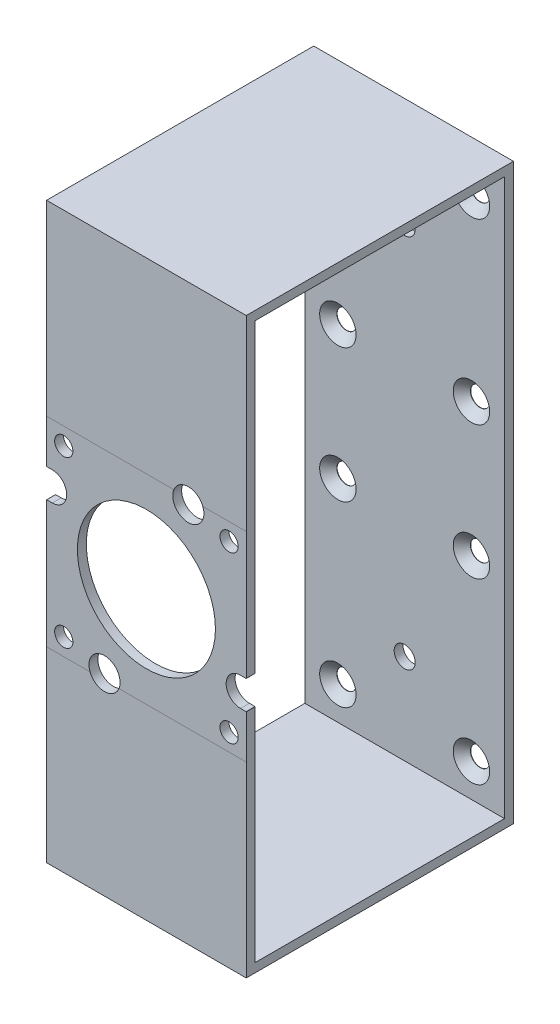
SolidWorks part; units mm, degrees
material "201 Annealed Stainless Steel (SS)"
ref_plane "Front Plane" through (0, 0, 0) normal (0, 0, 1) x (1, 0, 0)
ref_plane "Top Plane" through (0, 0, 0) normal (0, 1, 0) x (1, 0, 0)
ref_plane "Right Plane" through (0, 0, 0) normal (1, 0, 0) x (0, 0, -1)
sketch "Sketch2" plane through (0, 0, -4.819) normal (0, 0, -1) x (-1, 0, 0)
  circle A0 centre (-23.5732, -23.5732) radius 2.6 construction
  circle A1 centre (-23.5732, 23.5732) radius 2.6 construction
  circle A2 centre (23.5732, 23.5732) radius 2.6 construction
  circle A3 centre (23.5732, -23.5732) radius 2.6 construction
  circle A4 centre (-23.5732, -23.5732) radius 2.6
  circle A5 centre (-23.5732, 23.5732) radius 2.6
  circle A6 centre (23.5732, 23.5732) radius 2.6
  circle A7 centre (23.5732, -23.5732) radius 2.6
sketch "Sketch3" plane through (0, 0, -4.819) normal (0, 0, -1) x (-1, 0, 0)
  line L16 (28.4405, 7.8549) -> (26.8396, 7.8549)
  line L17 (26.8396, 16.0446) -> (28.4405, 16.0446)
  line L18 (28.4754, 16.0794) -> (28.4754, 25.845)
  line L19 (25.845, 28.4754) -> (-7.8201, 28.4754)
  line L20 (-7.8549, 28.4405) -> (-7.8549, 26.8396)
  line L21 (-16.0446, 26.8396) -> (-16.0446, 28.4405)
  line L22 (-16.0794, 28.4754) -> (-25.845, 28.4754)
  line L23 (-28.4754, 25.845) -> (-28.4754, -7.8201)
  line L24 (-28.4405, -7.8549) -> (-26.8396, -7.8549)
  line L25 (-26.8396, -16.0446) -> (-28.4405, -16.0446)
  line L26 (-28.4754, -16.0794) -> (-28.4754, -25.845)
  line L27 (-25.845, -28.4754) -> (7.8201, -28.4754)
  line L28 (7.8549, -28.4405) -> (7.8549, -26.8396)
  line L29 (16.0446, -26.8396) -> (16.0446, -28.4405)
  line L30 (16.0794, -28.4754) -> (25.845, -28.4754)
  line L31 (28.4754, -25.845) -> (28.4754, 7.8201)
  line L32 (28.4405, 7.8549) -> (26.8396, 7.8549)
  line L33 (26.8396, 16.0446) -> (28.4405, 16.0446)
  line L34 (28.4754, 16.0794) -> (28.4754, 25.845)
  line L35 (25.845, 28.4754) -> (-7.8201, 28.4754)
  line L36 (-7.8549, 28.4405) -> (-7.8549, 26.8396)
  line L37 (-16.0446, 26.8396) -> (-16.0446, 28.4405)
  line L38 (-16.0794, 28.4754) -> (-25.845, 28.4754)
  line L39 (-28.4754, 25.845) -> (-28.4754, -7.8201)
  line L40 (-28.4405, -7.8549) -> (-26.8396, -7.8549)
  line L41 (-26.8396, -16.0446) -> (-28.4405, -16.0446)
  line L42 (-28.4754, -16.0794) -> (-28.4754, -25.845)
  line L43 (-25.845, -28.4754) -> (7.8201, -28.4754)
  line L44 (7.8549, -28.4405) -> (7.8549, -26.8396)
  line L45 (16.0446, -26.8396) -> (16.0446, -28.4405)
  line L46 (16.0794, -28.4754) -> (25.845, -28.4754)
  line L47 (28.4754, -25.845) -> (28.4754, 7.8201)
  arc A8 (26.8396, 16.0446) -> (26.8396, 7.8549) centre (26.8396, 11.9498) ccw
  arc A9 (28.4754, 25.845) -> (25.845, 28.4754) centre (25.845, 25.845) ccw
  arc A10 (-16.0446, 26.8396) -> (-7.8549, 26.8396) centre (-11.9498, 26.8396) ccw
  arc A11 (-25.845, 28.4754) -> (-28.4754, 25.845) centre (-25.845, 25.845) ccw
  arc A12 (-26.8396, -16.0446) -> (-26.8396, -7.8549) centre (-26.8396, -11.9498) ccw
  arc A13 (-28.4754, -25.845) -> (-25.845, -28.4754) centre (-25.845, -25.845) ccw
  arc A14 (16.0446, -26.8396) -> (7.8549, -26.8396) centre (11.9498, -26.8396) ccw
  arc A15 (25.845, -28.4754) -> (28.4754, -25.845) centre (25.845, -25.845) ccw
  arc A16 (26.8396, 16.0446) -> (26.8396, 7.8549) centre (26.8396, 11.9498) ccw
  arc A17 (28.4754, 25.845) -> (25.845, 28.4754) centre (25.845, 25.845) ccw
  arc A18 (-16.0446, 26.8396) -> (-7.8549, 26.8396) centre (-11.9498, 26.8396) ccw
  arc A19 (-25.845, 28.4754) -> (-28.4754, 25.845) centre (-25.845, 25.845) ccw
  arc A20 (-26.8396, -16.0446) -> (-26.8396, -7.8549) centre (-26.8396, -11.9498) ccw
  arc A21 (-28.4754, -25.845) -> (-25.845, -28.4754) centre (-25.845, -25.845) ccw
  arc A22 (16.0446, -26.8396) -> (7.8549, -26.8396) centre (11.9498, -26.8396) ccw
  arc A23 (25.845, -28.4754) -> (28.4754, -25.845) centre (25.845, -25.845) ccw
  spline S8 degree 3 poles (-2168.2373, 2050.6322) (2176.4935, -2088.8807) (-2068.2203, 2155.8351) (2071.1385, -2188.738) knots -81.330068 -81.330068 -81.330068 -81.330068 81.328574 81.328574 81.328574 81.328574 only from (28.4754, 7.8201) to (28.4405, 7.8549)
  spline S9 degree 3 poles (2071.2526, 2212.7572) (-2068.2603, -2131.9736) (2176.4555, 2112.7403) (-2168.1176, -2026.6186) knots -78.188475 -78.188475 -78.188475 -78.188475 84.470167 84.470167 84.470167 84.470167 only from (28.4405, 16.0446) to (28.4754, 16.0794)
  spline S10 degree 3 poles (-2050.6322, -2168.2373) (2088.8807, 2176.4935) (-2155.8351, -2068.2203) (2188.738, 2071.1385) knots -81.330068 -81.330068 -81.330068 -81.330068 81.328574 81.328574 81.328574 81.328574 only from (-7.8201, 28.4754) to (-7.8549, 28.4405)
  spline S11 degree 3 poles (-2212.7572, 2071.2526) (2131.9736, -2068.2603) (-2112.7403, 2176.4555) (2026.6186, -2168.1176) knots -78.188475 -78.188475 -78.188475 -78.188475 84.470167 84.470167 84.470167 84.470167 only from (-16.0446, 28.4405) to (-16.0794, 28.4754)
  spline S12 degree 3 poles (2168.2373, -2050.6322) (-2176.4935, 2088.8807) (2068.2203, -2155.8351) (-2071.1385, 2188.738) knots -81.330068 -81.330068 -81.330068 -81.330068 81.328574 81.328574 81.328574 81.328574 only from (-28.4754, -7.8201) to (-28.4405, -7.8549)
  spline S13 degree 3 poles (-2071.2526, -2212.7572) (2068.2603, 2131.9736) (-2176.4555, -2112.7403) (2168.1176, 2026.6186) knots -78.188475 -78.188475 -78.188475 -78.188475 84.470167 84.470167 84.470167 84.470167 only from (-28.4405, -16.0446) to (-28.4754, -16.0794)
  spline S14 degree 3 poles (2050.6322, 2168.2373) (-2088.8807, -2176.4935) (2155.8351, 2068.2203) (-2188.738, -2071.1385) knots -81.330068 -81.330068 -81.330068 -81.330068 81.328574 81.328574 81.328574 81.328574 only from (7.8201, -28.4754) to (7.8549, -28.4405)
  spline S15 degree 3 poles (2212.7572, -2071.2526) (-2131.9736, 2068.2603) (2112.7403, -2176.4555) (-2026.6186, 2168.1176) knots -78.188475 -78.188475 -78.188475 -78.188475 84.470167 84.470167 84.470167 84.470167 only from (16.0446, -28.4405) to (16.0794, -28.4754)
  spline S16 degree 3 poles (28.4754, 7.8201) (28.4758, 7.8387) (28.4591, 7.8554) (28.4405, 7.8549) knots -0.784789 -0.784789 -0.784789 -0.784789 0.784789 0.784789 0.784789 0.784789
  spline S17 degree 3 poles (28.4405, 16.0446) (28.4591, 16.0441) (28.4758, 16.0608) (28.4754, 16.0794) knots 2.356803 2.356803 2.356803 2.356803 3.926382 3.926382 3.926382 3.926382
  spline S18 degree 3 poles (-7.8201, 28.4754) (-7.8387, 28.4758) (-7.8554, 28.4591) (-7.8549, 28.4405) knots -0.784789 -0.784789 -0.784789 -0.784789 0.784789 0.784789 0.784789 0.784789
  spline S19 degree 3 poles (-16.0446, 28.4405) (-16.0441, 28.4591) (-16.0608, 28.4758) (-16.0794, 28.4754) knots 2.356803 2.356803 2.356803 2.356803 3.926382 3.926382 3.926382 3.926382
  spline S20 degree 3 poles (-28.4754, -7.8201) (-28.4758, -7.8387) (-28.4591, -7.8554) (-28.4405, -7.8549) knots -0.784789 -0.784789 -0.784789 -0.784789 0.784789 0.784789 0.784789 0.784789
  spline S21 degree 3 poles (-28.4405, -16.0446) (-28.4591, -16.0441) (-28.4758, -16.0608) (-28.4754, -16.0794) knots 2.356803 2.356803 2.356803 2.356803 3.926382 3.926382 3.926382 3.926382
  spline S22 degree 3 poles (7.8201, -28.4754) (7.8387, -28.4758) (7.8554, -28.4591) (7.8549, -28.4405) knots -0.784789 -0.784789 -0.784789 -0.784789 0.784789 0.784789 0.784789 0.784789
  spline S23 degree 3 poles (16.0446, -28.4405) (16.0441, -28.4591) (16.0608, -28.4758) (16.0794, -28.4754) knots 2.356803 2.356803 2.356803 2.356803 3.926382 3.926382 3.926382 3.926382
  dimension "D1" = 0
extrude "Boss-Extrude1" add sketch "Sketch3" along normal blind 2.54 contours L35 S18 L36 A18 L37 S19 L38 A19 L39 S20 L40 A20 L41 S21 L42 A21 L43 S22 L44 A22 L45 S23 L46 A23 L47 S16 L32 A16 L33 S17 L34 A17
extrude "Cut-Extrude1" cut sketch "Sketch2" against normal through all and the other way through all contours A7 | A4 | A5 | A6
sketch "Sketch4" plane through (0, 0, -4.819) normal (0, 0, 1) x (1, 0, 0)
  line L0 (-28.4754, 25.845) -> (-28.4754, 79.2754)
  line L1 (-28.4754, 79.2754) -> (28.4754, 79.2754)
  line L2 (28.4754, 79.2754) -> (28.4754, 25.845)
  line L3 (-28.4754, -25.845) -> (-28.4754, -79.2754)
  line L4 (-28.4754, -79.2754) -> (28.4754, -79.2754)
  line L5 (28.4754, -79.2754) -> (28.4754, -25.845)
  line L6 (-25.845, 28.4754) -> (7.8201, 28.4754) construction
  line L7 (25.845, -28.4754) -> (-7.8201, -28.4754) construction
  line L8 (-25.845, 28.4754) -> (25.845, 28.4754)
  line L9 (25.845, -28.4754) -> (-25.845, -28.4754)
  arc A0 (-25.845, 28.4754) -> (-28.4754, 25.845) centre (-25.845, 25.845) ccw construction
  arc A1 (25.845, -28.4754) -> (28.4754, -25.845) centre (25.845, -25.845) ccw construction
  arc A2 (-25.845, 28.4754) -> (-28.4754, 25.845) centre (-25.845, 25.845) ccw
  arc A3 (25.845, -28.4754) -> (28.4754, -25.845) centre (25.845, -25.845) ccw
  arc A4 (-28.4754, -25.845) -> (-25.845, -28.4754) centre (-25.845, -25.845) ccw construction
  arc A5 (28.4754, 25.845) -> (25.845, 28.4754) centre (25.845, 25.845) ccw construction
  arc A6 (-28.4754, -25.845) -> (-25.845, -28.4754) centre (-25.845, -25.845) ccw
  arc A7 (28.4754, 25.845) -> (25.845, 28.4754) centre (25.845, 25.845) ccw
  arc M5 (-25.845, 28.4754) -> (-28.4754, 25.845) centre (-25.845, 25.845) ccw
  line M20 (-7.8201, -28.4754) -> (25.845, -28.4754)
  arc M21 (25.845, -28.4754) -> (28.4754, -25.845) centre (25.845, -25.845) ccw
  spline M35 degree 3 poles (7.8549, 28.4405) (7.8554, 28.4591) (7.8387, 28.4758) (7.8201, 28.4754) knots -0.784789 -0.784789 -0.784789 -0.784789 0.784789 0.784789 0.784789 0.784789
  line M36 (7.8201, 28.4754) -> (-25.845, 28.4754)
  dimension "D1" = 50.8
  dimension "D2" = 50.8
extrude "Boss-Extrude2" add sketch "Sketch4" against normal blind 2.54 contours L2 L1 L0 M5 M36 M35 | L4 L5 L3 M21 M20
sketch "Sketch5" plane through (0, 0, -4.819) normal (0, 0, 1) x (1, 0, 0)
  circle A0 centre (0, 0) radius 19.685
  dimension "D1" = 39.37
extrude "Cut-Extrude2" cut sketch "Sketch5" against normal blind 2.54
sketch "Sketch6" plane through (0, 79.2754, 0) normal (0, 1, 0) x (1, 0, 0)
  line L0 (-28.4754, 4.819) -> (-28.4754, 81.019)
  line L1 (-28.4754, 81.019) -> (28.4754, 81.019)
  line L2 (28.4754, 81.019) -> (28.4754, 4.819)
  line L3 (-28.4754, 4.819) -> (28.4754, 4.819)
  line L4 (7.8549, 4.819) -> (16.0446, 4.819) construction
  dimension "D1" = 76.2
extrude "Boss-Extrude3" add sketch "Sketch6" along normal blind 2.54
sketch "Sketch7" plane through (0, -79.2754, 0) normal (0, -1, 0) x (1, 0, 0)
  line L0 (-28.4754, -4.819) -> (-28.4754, -81.019)
  line L1 (-28.4754, -81.019) -> (28.4754, -81.019) construction
  line L2 (-28.4754, -81.019) -> (28.4754, -81.019)
  line L3 (28.4754, -81.019) -> (28.4754, -4.819)
  line L4 (28.4754, -4.819) -> (-28.4754, -4.819)
extrude "Boss-Extrude5" add sketch "Sketch7" along normal blind 2.54 contours L2 L3 L4 L0
sketch "Sketch8" plane through (0, -79.2754, 0) normal (0, 1, 0) x (1, 0, 0)
  line L0 (28.4754, 81.019) -> (28.4754, 7.359) construction
  line L1 (-28.4754, 81.019) -> (28.4754, 81.019)
  line L2 (-28.4754, 81.019) -> (-28.4754, 78.479)
  line L3 (-28.4754, 78.479) -> (28.4754, 78.479)
  line L4 (28.4754, 81.019) -> (28.4754, 78.479)
  dimension "D1" = 2.54
sketch "Sketch10" plane through (0, 79.2754, 0) normal (0, -1, 0) x (1, 0, 0)
  line L0 (28.4754, -7.359) -> (28.4754, -81.019) construction
  line L1 (-28.4754, -81.019) -> (28.4754, -81.019)
  line L2 (-28.4754, -81.019) -> (-28.4754, -78.479)
  line L3 (-28.4754, -78.479) -> (28.4754, -78.479)
  line L4 (28.4754, -81.019) -> (28.4754, -78.479)
  dimension "D1" = 2.54
loft "Loft1" add profiles "Sketch10", "Sketch8"
sketch "Sketch11" plane through (0, 0, -4.819) normal (0, 0, 1) x (1, 0, 0)
  line L0 (28.4754, 28.4754) -> (-28.4754, 28.4754)
  line L1 (-28.4754, 16.0794) -> (-28.4754, 81.8154) construction
  line L2 (-28.4754, -28.4754) -> (28.4754, -28.4754)
  line L3 (28.4754, -16.0794) -> (28.4754, -81.8154) construction
  line L4 (-28.4754, -81.8154) -> (-28.4754, 7.8201) construction
  line L5 (28.4754, 81.8154) -> (28.4754, -7.8201) construction
  line L6 (7.8209, 28.4754) -> (16.0789, 28.4754) construction
  line L7 (-7.8209, -28.4754) -> (-16.0789, -28.4754) construction
split line "Split Line1"
sketch "Sketch12" plane through (0, 0, -4.819) normal (0, 0, 1) x (1, 0, 0)
  circle A0 centre (-11.9498, -26.8396) radius 4.4411
  circle A1 centre (11.9498, 26.8396) radius 4.4411
  arc A2 (7.8549, 26.8396) -> (16.0446, 26.8396) centre (11.9498, 26.8396) ccw construction
extrude "Cut-Extrude3" cut sketch "Sketch12" against normal up to next
sketch "Sketch13" plane through (0, 0, -81.019) normal (0, 0, -1) x (-1, 0, 0)
  line L0 (-28.4754, 0) -> (28.4754, 0) construction
  line L1 (-19.05, 19.05) -> (19.05, 19.05) construction
  line L2 (-19.05, 19.05) -> (-19.05, 69.85) construction
  line L3 (-19.05, 69.85) -> (19.05, 69.85) construction
  line L4 (19.05, 19.05) -> (19.05, 69.85) construction
  line L5 (-19.05, 19.05) -> (19.05, 69.85) construction
  line L6 (-19.05, 69.85) -> (19.05, 19.05) construction
  line L7 (28.4754, 81.8154) -> (28.4754, -81.8154) construction
  line L8 (-19.05, -69.85) -> (19.05, -19.05) construction
  line L9 (-19.05, -19.05) -> (19.05, -69.85) construction
  line L10 (19.05, -19.05) -> (19.05, -69.85) construction
  line L11 (-19.05, -69.85) -> (19.05, -69.85) construction
  line L12 (-19.05, -19.05) -> (-19.05, -69.85) construction
  line L13 (-19.05, -19.05) -> (19.05, -19.05) construction
  point P0 (0, 44.45)
  point P11 (0, 0)
  point P17 (0, -44.45)
  dimension "D1" = 50.8
  dimension "D2" = 38.1
  dimension "D3" = 19.05
sketch "Sketch18" plane through (0, 0, -78.479) normal (0, 0, 1) x (1, 0, 0)
  line L0 (19.05, -19.05) -> (19.05, -69.85) construction
  line L1 (19.05, -69.85) -> (-19.05, -69.85) construction
  line L2 (-19.05, -19.05) -> (-19.05, -69.85) construction
  line L3 (19.05, -19.05) -> (-19.05, -19.05) construction
  line L4 (19.05, 19.05) -> (-19.05, 19.05) construction
  line L5 (-19.05, 19.05) -> (-19.05, 69.85) construction
  line L6 (19.05, 69.85) -> (-19.05, 69.85) construction
  line L7 (19.05, 19.05) -> (19.05, 69.85) construction
  line L8 (19.05, -19.05) -> (19.05, -69.85) construction
  line L9 (19.05, -69.85) -> (-19.05, -69.85) construction
  line L10 (-19.05, -19.05) -> (-19.05, -69.85) construction
  line L11 (19.05, -19.05) -> (-19.05, -19.05) construction
  line L12 (19.05, 19.05) -> (-19.05, 19.05) construction
  line L13 (-19.05, 19.05) -> (-19.05, 69.85) construction
  line L14 (19.05, 69.85) -> (-19.05, 69.85) construction
  line L15 (19.05, 19.05) -> (19.05, 69.85) construction
hole_wizard "CSK for M5 Flat Head Machine Screw1" positions "Sketch19" profile "Sketch20" countersink size "M5" standard "ANSI Metric" end condition through all
sketch "Sketch19" plane through (0, 0, -78.479) normal (0, 0, 1) x (1, 0, 0)
  point P0 (-19.05, 69.85)
  point P3 (19.05, 69.85)
  point P6 (-19.05, 19.05)
  point P9 (19.05, 19.05)
  point P12 (-19.05, -19.05)
  point P15 (19.05, -19.05)
  point P18 (-19.05, -69.85)
  point P21 (19.05, -69.85)
sketch "Sketch20" plane through (-19.05, 69.85, -78.479) normal (1, 0, 0) x (0, -1, 0)
  line L0 (0, 0) -> (0, 2.54)
  line L1 (0, 2.54) -> (2.75, 2.54)
  line L2 (2.75, 2.54) -> (2.75, 2.45)
  line L3 (2.75, 2.45) -> (5.2, 0)
  line L5 (5.2, 0) -> (0, 0)
  line L6 (-2.75, 2.45) -> (-5.2, 0) construction
  line L11 (0, -6.35) -> (0, 107.95) construction
  dimension "Thru Hole Dia." = 5.5
  dimension "Thru Hole Depth" = 2.54
  dimension "Near C'Sink Dia." = 10.4
  dimension "Near C'Sink Angle" = 90
sketch "Sketch26" plane through (0, 0, -78.479) normal (0, 0, 1) x (1, 0, 0)
  line L0 (0, -53.5) -> (0, 53.5) construction
  circle A0 centre (0, 53.5) radius 3
  circle A1 centre (0, -53.5) radius 3
  point P4 (0, 0)
  point P5 (0, 0)
  point P7 (0, 0)
  dimension "D2" = 6
  dimension "D1" = 107
extrude "Cut-Extrude5" cut sketch "Sketch26" against normal blind 10
